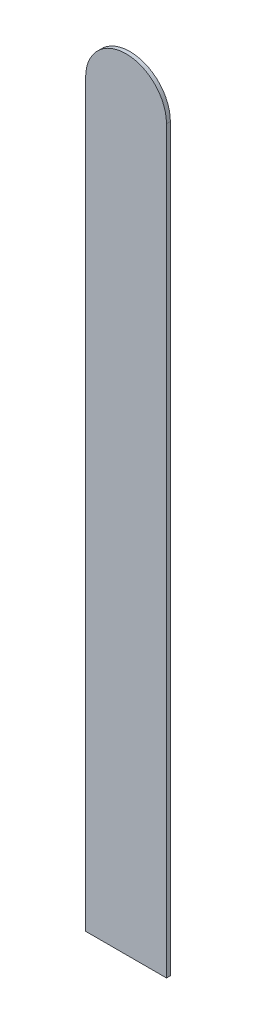
SolidWorks part; units mm, degrees
material "PP Film"
ref_plane "Front Plane" through (0, 0, 0) normal (0, 0, 1) x (1, 0, 0)
ref_plane "Top Plane" through (0, 0, 0) normal (0, 1, 0) x (1, 0, 0)
ref_plane "Right Plane" through (0, 0, 0) normal (1, 0, 0) x (0, 0, -1)
sketch "Sketch2" plane through (0, 0, 0) normal (0, 0, 1) x (1, 0, 0)
  line L1 (-6.35, 0) -> (-6.35, 70.6374) construction
  line L3 (0, 70.6374) -> (0, 12.5222)
  line L4 (0, 12.5222) -> (-6.35, 12.5222)
  line L5 (-6.35, 70.6374) -> (-6.35, 12.5222)
  arc A0 (0, 70.6374) -> (-6.35, 70.6374) centre (-3.175, 70.6374) ccw
  arc A3 (0, 70.6374) -> (-6.35, 70.6374) centre (-3.175, 70.6374) ccw construction
  dimension "D1" = 58.1152
extrude "Boss-Extrude1" add sketch "Sketch2" along normal blind 0.3048
